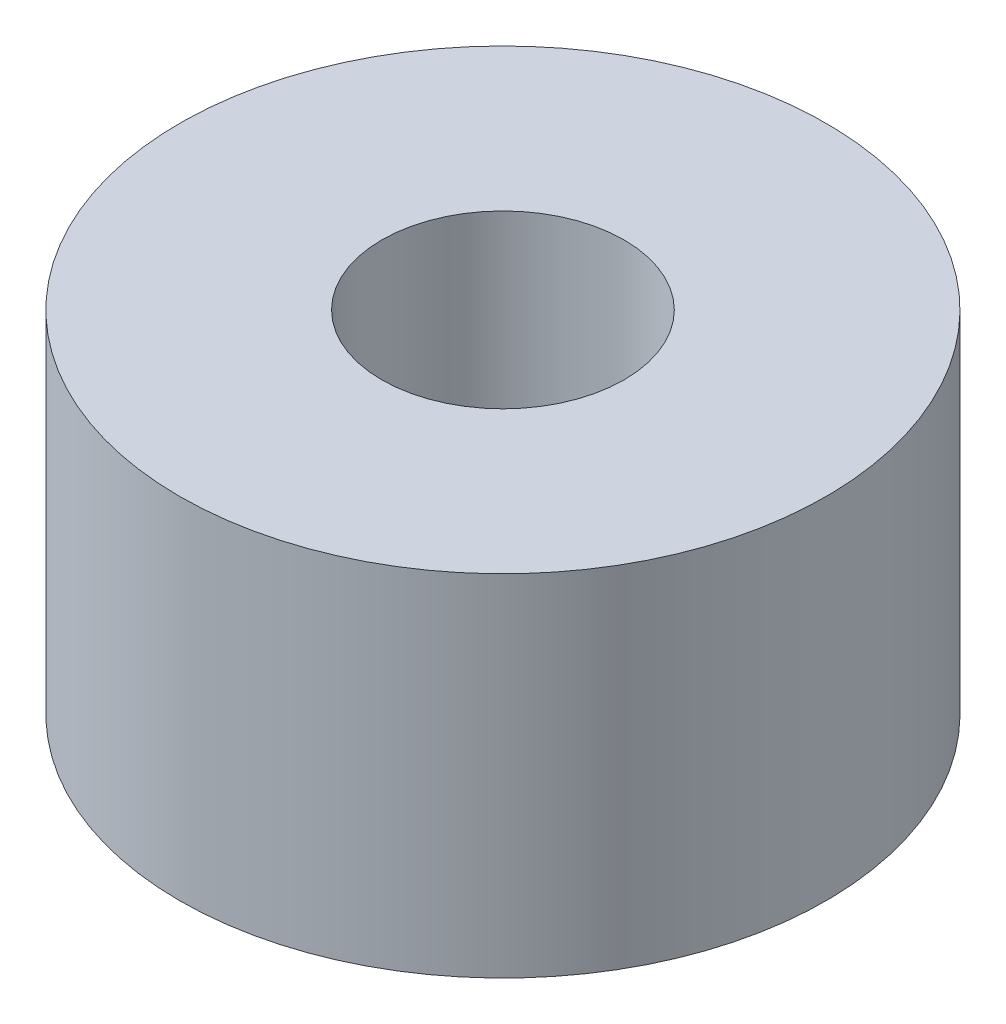
SolidWorks part; units mm, degrees
ref_plane "Front Plane" through (0, 0, 0) normal (0, 0, 1) x (1, 0, 0)
ref_plane "Top Plane" through (0, 0, 0) normal (0, 1, 0) x (1, 0, 0)
ref_plane "Right Plane" through (0, 0, 0) normal (1, 0, 0) x (0, 0, -1)
sketch "Sketch1" plane through (0, 0, 0) normal (0, 1, 0) x (1, 0, 0)
  circle A0 centre (0, 0) radius 12.7
  circle A1 centre (0, 0) radius 4.7625
  dimension "D1" = 9.525
  dimension "D2" = 25.4
extrude "Boss-Extrude1" add sketch "Sketch1" along normal blind 13.7588 contours A0 A1
